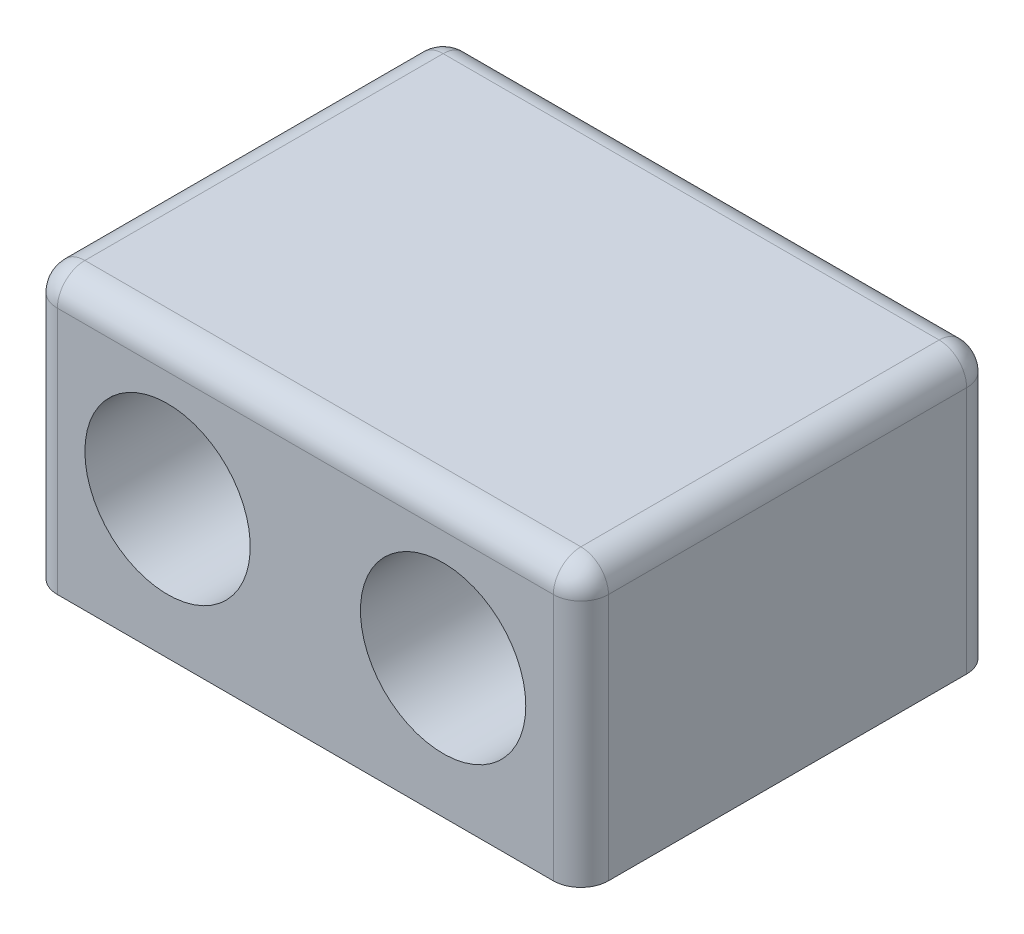
SolidWorks part; units mm, degrees
ref_plane "Front Plane" through (0, 0, 0) normal (0, 0, 1) x (1, 0, 0)
ref_plane "Top Plane" through (0, 0, 0) normal (0, 1, 0) x (1, 0, 0)
ref_plane "Right Plane" through (0, 0, 0) normal (1, 0, 0) x (0, 0, -1)
sketch "Sketch1" plane through (0, 0, 0) normal (0, 1, 0) x (1, 0, 0)
  line L1 (-10, -7.5) -> (10, -7.5)
  line L2 (-10, -7.5) -> (-10, 7.5)
  line L3 (-10, 7.5) -> (10, 7.5)
  line L4 (10, -7.5) -> (10, 7.5)
  line L5 (-10, -7.5) -> (10, 7.5) construction
  line L6 (-10, 7.5) -> (10, -7.5) construction
  point P0 (0, 0)
  dimension "D1" = 20
  dimension "D2" = 15
extrude "Boss-Extrude1" add sketch "Sketch1" along normal blind 10
sketch "Sketch4" plane through (0, 0, 7.5) normal (0, 0, 1) x (1, 0, 0)
  line L0 (10, 10) -> (10, 0) construction
  line L1 (-10, 10) -> (10, 10) construction
  circle A0 centre (5, 5) radius 3
  dimension "D1" = 6
  dimension "D2" = 5
  dimension "D3" = 5
extrude "Cut-Extrude1" cut sketch "Sketch4" against normal blind 8
sketch "Sketch6" plane through (0, 0, -0.5) normal (0, 0, 1) x (1, 0, 0)
  line L0 (3.75, 5) -> (6.25, 5) construction
  line L1 (3.75, 5.75) -> (6.25, 5.75)
  line L2 (3.75, 4.25) -> (6.25, 4.25)
  arc A0 (3.75, 5.75) -> (3.75, 4.25) centre (3.75, 5) ccw
  arc A1 (6.25, 4.25) -> (6.25, 5.75) centre (6.25, 5) ccw
  point P2 (5, 5)
  dimension "D2" = 0.75
  dimension "D1" = 2.5
extrude "Cut-Extrude2" cut sketch "Sketch6" against normal through all
mirror "Mirror1" about plane through (0, 0, 0) normal (1, 0, 0) of "Cut-Extrude1", "Cut-Extrude2"
fillet "Fillet1" radius 1 8 edges at (0, 10, 7.5) (-10, 10, 0) (0, 10, -7.5) (10, 10, 0) (10, 5, -7.5) (-10, 5, -7.5) (10, 5, 7.5) (-10, 5, 7.5)
